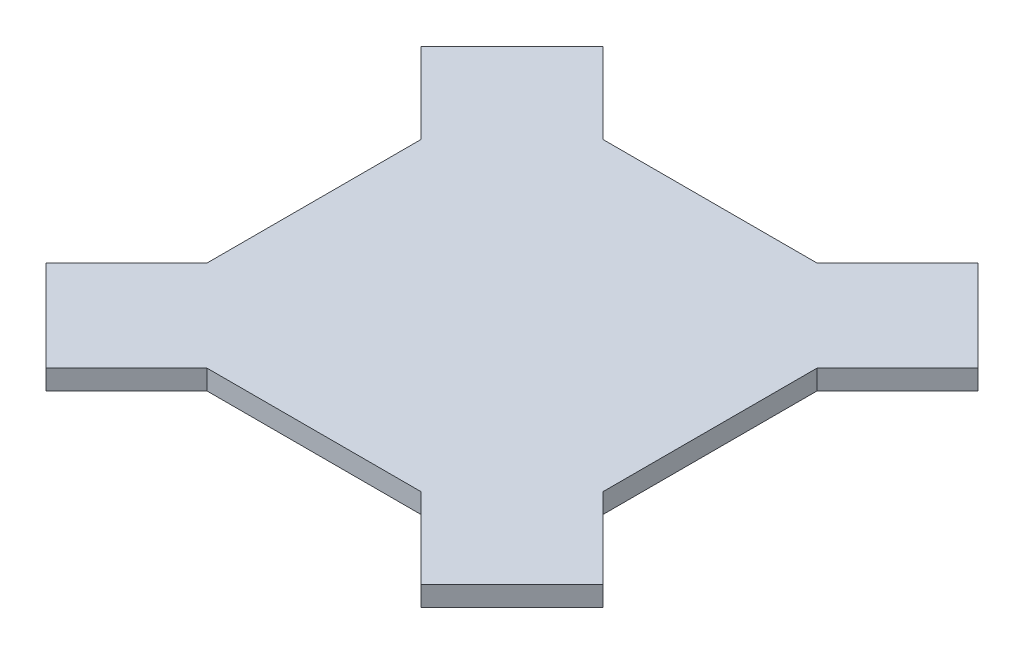
SolidWorks part; units mm, degrees
ref_plane "Front Plane" through (0, 0, 0) normal (0, 0, 1) x (1, 0, 0)
ref_plane "Top Plane" through (0, 0, 0) normal (0, 1, 0) x (1, 0, 0)
ref_plane "Right Plane" through (0, 0, 0) normal (1, 0, 0) x (0, 0, -1)
sketch "Sketch1" plane through (0, 0, 0) normal (0, 1, 0) x (1, 0, 0)
  line L36 (-40, -40) -> (40, -40)
  line L37 (-40, -40) -> (-40, 40)
  line L38 (-40, 40) -> (40, 40)
  line L39 (40, -40) -> (40, 40)
  line L40 (-40, -40) -> (40, 40) construction
  line L41 (-40, 40) -> (40, -40) construction
  point P0 (0, 0)
  point P2 (0, 52.499)
  point P5 (4.6403, 57.1393)
  point P6 (170.7183, -59.5051)
  point P7 (-49.3664, 101.8654)
  point P8 (-44.7261, 106.5057)
  point P9 (160.1117, -70.1117)
  point P10 (-69.6397, 159.6397)
  point P13 (-59.0331, 170.2463)
  point P14 (149.5051, -80.7183)
  point P15 (-80.2463, 149.0331)
  point P16 (152.7581, 131.8855)
  point P17 (-52.3831, -73.2557)
  point P18 (131.5449, 153.0987)
  point P19 (-73.5963, -52.0425)
extrude "Boss-Extrude1" add sketch "Sketch1" along normal blind 4
sketch "Sketch2" plane through (0, 4, 0) normal (0, 1, 0) x (1, 0, 0)
  line L5 (37.8787, -56.2635) -> (-56.2635, 37.8787)
  line L6 (37.8787, -56.2635) -> (56.2635, -37.8787)
  line L11 (-56.2635, 37.8787) -> (-37.8787, 56.2635)
  line L12 (56.2635, -37.8787) -> (-37.8787, 56.2635)
  line L13 (37.8787, -56.2635) -> (-37.8787, 56.2635) construction
  line L14 (-56.2635, 37.8787) -> (56.2635, -37.8787) construction
  line L16 (-37.8787, -56.2635) -> (56.2635, 37.8787)
  line L17 (-37.8787, -56.2635) -> (-56.2635, -37.8787)
  line L18 (56.2635, 37.8787) -> (37.8787, 56.2635)
  line L19 (-56.2635, -37.8787) -> (37.8787, 56.2635)
  line L20 (-37.8787, -56.2635) -> (37.8787, 56.2635) construction
  line L21 (56.2635, 37.8787) -> (-56.2635, -37.8787) construction
  point P0 (-40, 40)
  point P3 (-47.0711, 47.0711)
  point P4 (0, 0)
  point P14 (47.0711, 47.0711)
  point P15 (0, 0)
  dimension "D1" = 10
  dimension "D2" = 26
  dimension "D3" = 10
  dimension "D4" = 26
  dimension "D5" = 10
  dimension "D6" = 10
extrude "Boss-Extrude2" add sketch "Sketch2" against normal blind 4 contours L12 L11 L5 M19 M20 | L19 L17 L16 M21 M20 | L19 L16 L18 M19 M18 | L6 L12 L5 M18 M21
